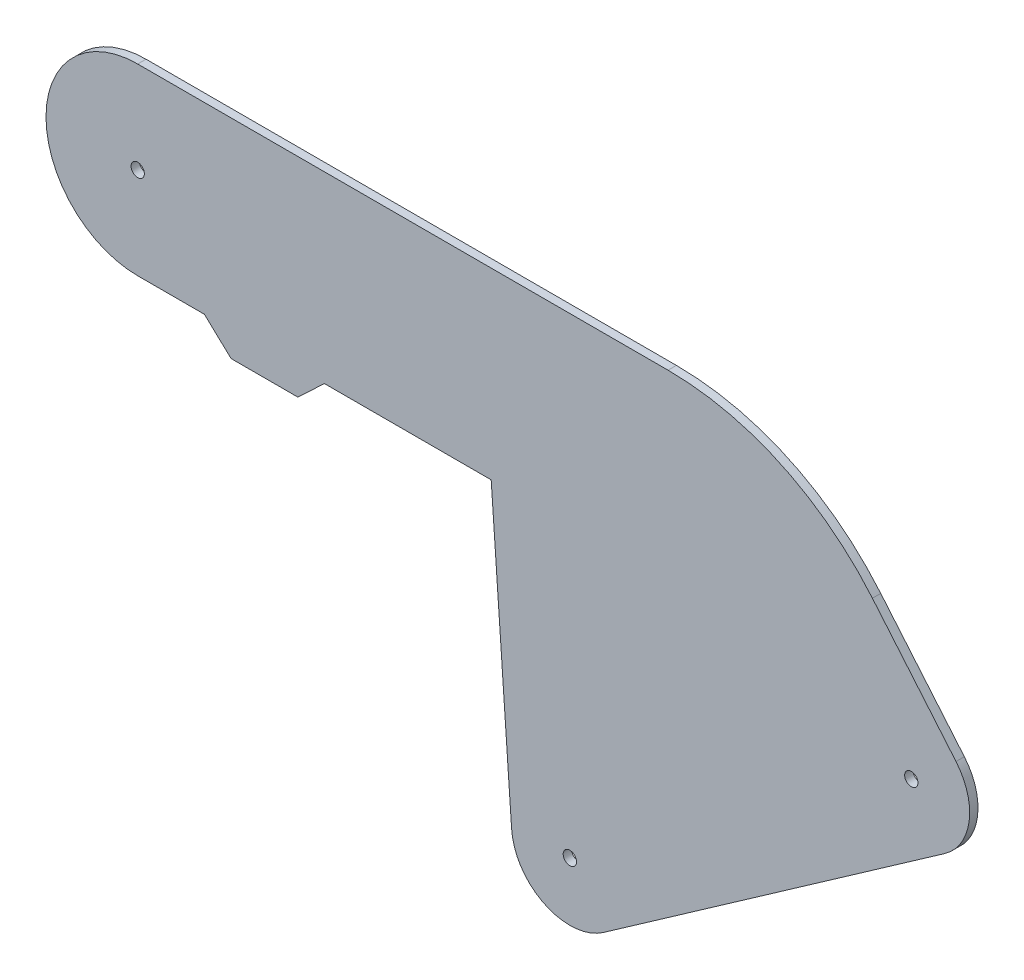
SolidWorks part; units mm, degrees
material "ABS PC"
ref_plane "Front Plane" through (0, 0, 0) normal (0, 0, 1) x (1, 0, 0)
ref_plane "Top Plane" through (0, 0, 0) normal (0, 1, 0) x (1, 0, 0)
ref_plane "Right Plane" through (0, 0, 0) normal (1, 0, 0) x (0, 0, -1)
sketch "Sketch1" plane through (0, 0, 0) normal (0, 0, 1) x (1, 0, 0)
  line L0 (0, 0) -> (0, 215.9) construction
  line L1 (133.35, 0) -> (133.35, 171.45) construction
  line L2 (0.0421, 0) -> (133.3921, 0) construction
  line L3 (50.8, 0) -> (50.8, 123.825) construction
  line L4 (508, 0) -> (508, 50000) construction
  line L11 (133.35, 171.45) -> (0, 171.45) construction
  line L20 (508, 457.2) -> (482.6, 457.2) construction
  line L22 (-203.2, 0) -> (-203.2, 53.1862) construction
  line L31 (-203.2, 520.7) -> (50.8, 520.7) construction
  line L48 (294.6125, 162.3041) -> (164.5721, 71.2488) construction
  line L52 (0, 180.975) -> (134.62, 180.975) construction
  line L53 (134.62, 180.975) -> (142.4012, 69.6985)
  line L62 (177.3198, 53.0432) -> (307.3602, 144.0984)
  line L66 (25.4, 180.975) -> (35.56, 171.45)
  line L67 (35.56, 171.45) -> (60.96, 171.45)
  line L68 (60.96, 171.45) -> (71.12, 180.975)
  line L69 (71.12, 180.975) -> (134.62, 180.975)
  line L70 (0, 250.825) -> (201.9704, 250.825)
  line L71 (279.8005, 214.5322) -> (311.6378, 176.59)
  line L72 (0, 180.975) -> (25.4, 180.975)
  circle A11 centre (508, 75.057) radius 75.057 construction
  arc A19 (0, 250.825) -> (0, 180.975) centre (0, 215.9) ccw
  circle A23 centre (294.6125, 162.3041) radius 2.54
  circle A24 centre (164.5721, 71.2488) radius 2.54
  circle A25 centre (0, 215.9) radius 2.54
  arc A28 (201.9704, 250.825) -> (279.8005, 214.5322) centre (201.9704, 149.225) cw
  circle A29 centre (294.6125, 162.3041) radius 12.7 construction
  arc A32 (311.6378, 176.59) -> (307.3602, 144.0984) centre (294.6125, 162.3041) cw
  circle A33 centre (164.5721, 71.2488) radius 12.7 construction
  arc A34 (142.4012, 69.6985) -> (177.3198, 53.0432) centre (164.5721, 71.2488) ccw
  point P2 (0, 0)
  point P10 (202.806, 253.6406)
  point P17 (-177.8, 889)
  point P27 (177.3198, 53.0432)
  point P38 (201.9704, 250.825)
  point P42 (134.62, 180.975)
  dimension "D4" = 304.8
  dimension "D9" = 49.53
  dimension "D10" = 134.62
  dimension "D11" = 158.75
  dimension "D12" = 59
  dimension "D13" = 150.114
  dimension "D14" = 94
  dimension "D21" = 25.4
  dimension "D3" = 171.45
  dimension "D6" = 130
  dimension "D15" = 25.4
  dimension "D23" = 25.4
  dimension "D8" = 69.85
  dimension "D28" = 5.08
  dimension "D29" = 9.525
  dimension "D30" = 101.6
  dimension "D24" = 22.225
  dimension "D26" = 25.4
  dimension "D1" = 82.55
  dimension "D2" = 215.9
  dimension "D5" = 50.8
  dimension "D7" = 457.2
  dimension "D17" = 457.2
  dimension "D18" = 177.8
  dimension "D19" = 889
  dimension "D20" = 25.4
  dimension "4.5" = 203.2
  dimension "D27" = 63.5
extrude "Boss-Extrude1" add sketch "Sketch1" along normal blind 3.175
